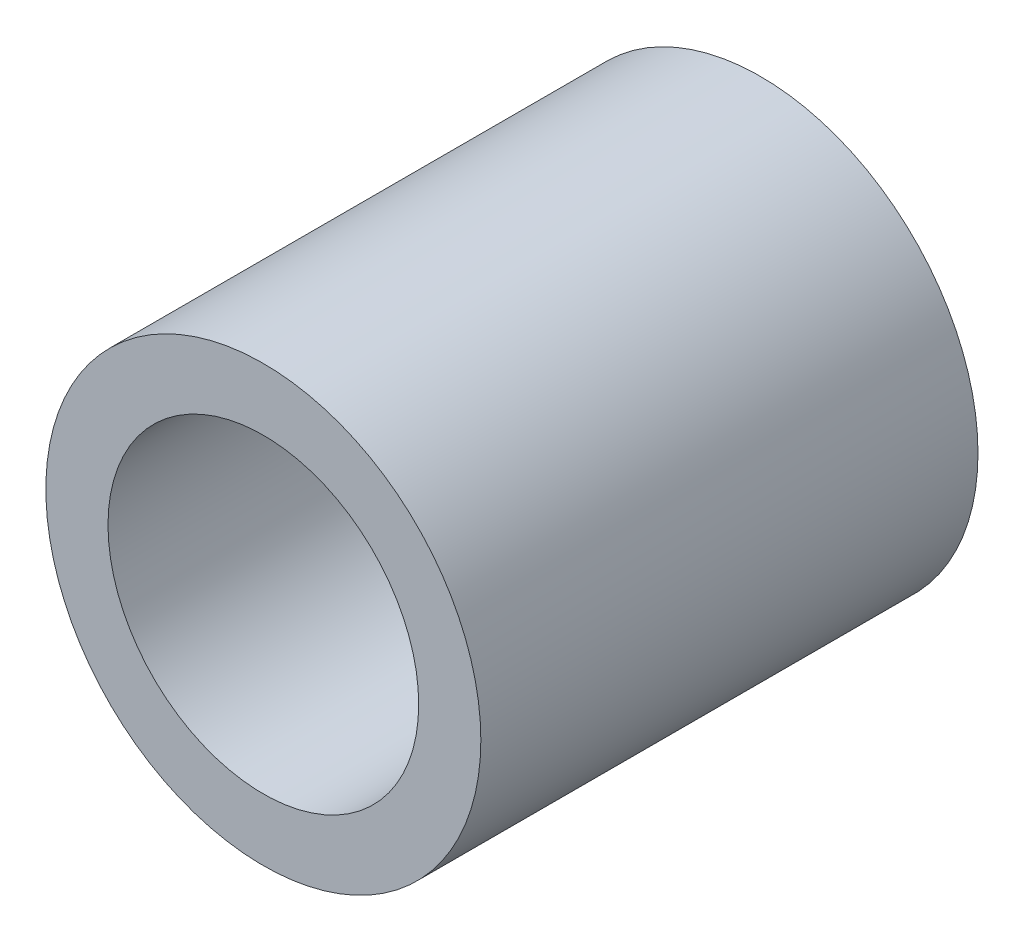
SolidWorks part; units mm, degrees
material "5052-H32"
ref_plane "Front Plane" through (0, 0, 0) normal (0, 0, 1) x (1, 0, 0)
ref_plane "Top Plane" through (0, 0, 0) normal (0, 1, 0) x (1, 0, 0)
ref_plane "Right Plane" through (0, 0, 0) normal (1, 0, 0) x (0, 0, -1)
sketch "Sketch1" plane through (0, 0, 0) normal (0, 0, 1) x (1, 0, 0)
  circle A0 centre (0, 0) radius 3.5
  circle A1 centre (0, 0) radius 2.5
  dimension "D1" = 5
  dimension "D2" = 7
extrude "Boss-Extrude1" add sketch "Sketch1" along normal blind 8
